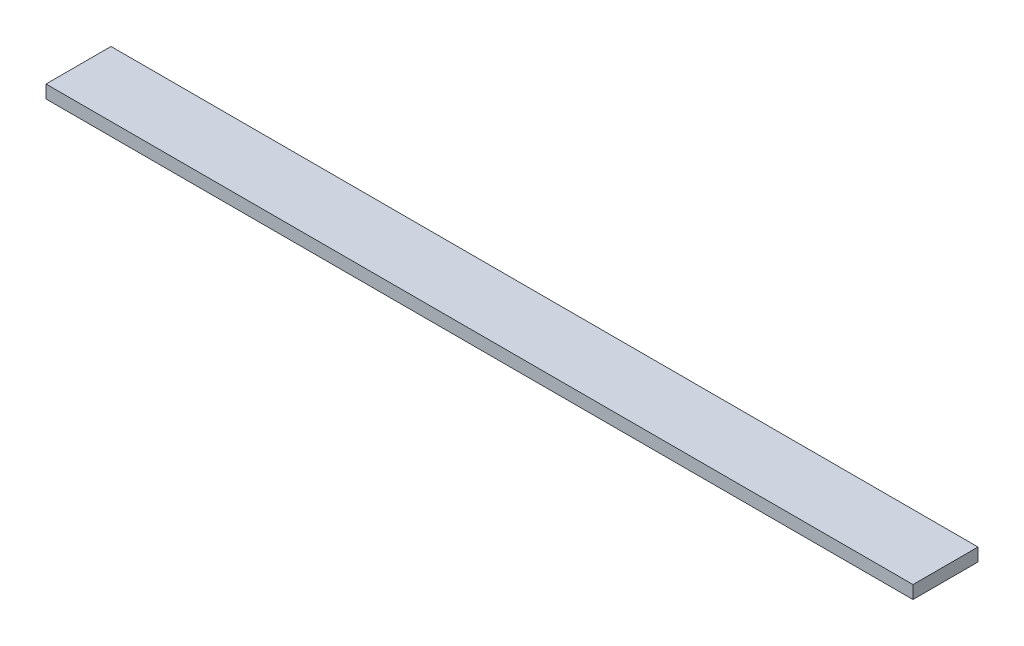
SolidWorks part; units mm, degrees
ref_plane "Спереди" through (0, 0, 0) normal (0, 0, 1) x (1, 0, 0)
ref_plane "Сверху" through (0, 0, 0) normal (0, 1, 0) x (1, 0, 0)
ref_plane "Справа" through (0, 0, 0) normal (1, 0, 0) x (0, 0, -1)
sketch "Эскиз1" plane through (0, 0, 0) normal (1, 0, 0) x (0, 0, -1)
  line L1 (-7.5, -1.5) -> (7.5, -1.5)
  line L2 (-7.5, -1.5) -> (-7.5, 1.5)
  line L3 (-7.5, 1.5) -> (7.5, 1.5)
  line L4 (7.5, -1.5) -> (7.5, 1.5)
  line L5 (-7.5, -1.5) -> (7.5, 1.5) construction
  line L6 (-7.5, 1.5) -> (7.5, -1.5) construction
  point P0 (0, 0)
  dimension "D1" = 3
  dimension "D2" = 15
extrude "Бобышка-Вытянуть1" add sketch "Эскиз1" along normal blind 200
